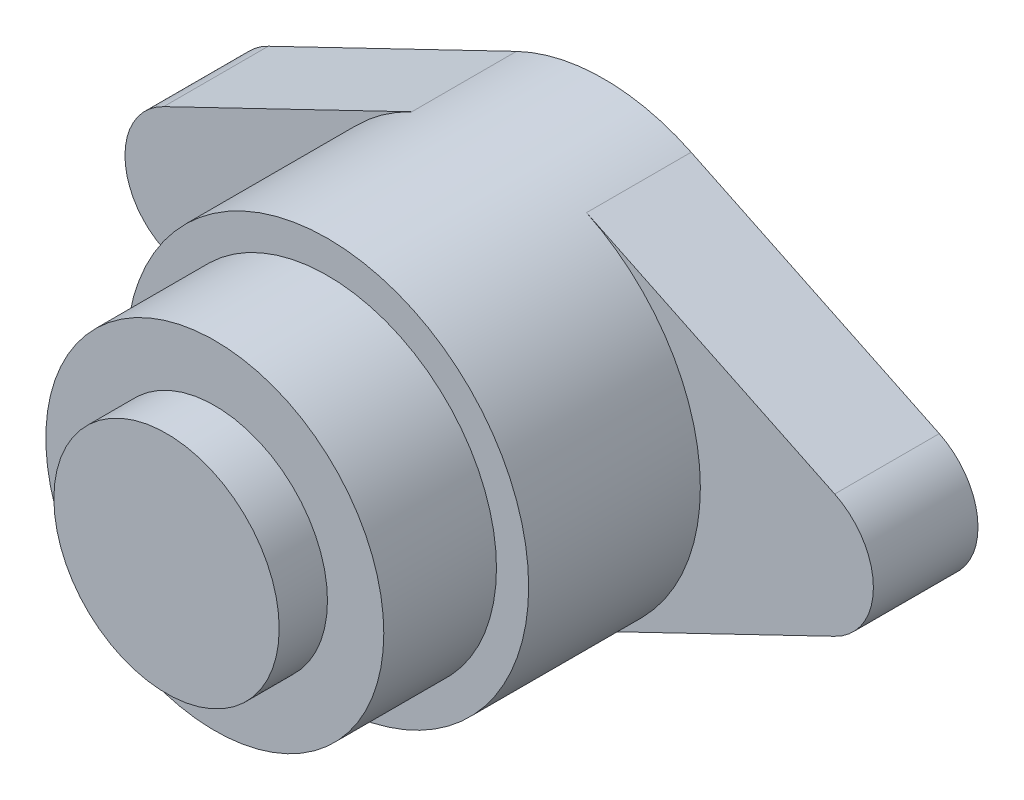
SolidWorks part; units mm, degrees
ref_plane "Front Plane" through (0, 0, 0) normal (0, 0, 1) x (1, 0, 0)
ref_plane "Top Plane" through (0, 0, 0) normal (0, 1, 0) x (1, 0, 0)
ref_plane "Right Plane" through (0, 0, 0) normal (1, 0, 0) x (0, 0, -1)
sketch "Sketch1" plane through (0, 0, 0) normal (0, 0, 1) x (1, 0, 0)
  line L0 (-19, 0) -> (19, 0) construction
  line L1 (-20.8454, 3.8284) -> (-5.4276, 11.2601)
  line L2 (-20.8454, -3.8284) -> (-5.4276, -11.2601)
  line L3 (5.4276, 11.2601) -> (20.8454, 3.8284)
  line L4 (5.4276, -11.2601) -> (20.8454, -3.8284)
  arc A1 (-20.8454, 3.8284) -> (-20.8454, -3.8284) centre (-19, 0) ccw
  arc A2 (20.8454, -3.8284) -> (20.8454, 3.8284) centre (19, 0) ccw
  arc A3 (-5.4276, -11.2601) -> (5.4276, -11.2601) centre (0, 0) ccw
  arc A4 (-5.4276, 11.2601) -> (5.4276, 11.2601) centre (0, 0) cw
  point P0 (0, -12.5)
  point P4 (0, 12.5)
  point P6 (-23.25, 0)
  point P7 (0, 0)
  point P14 (23.25, 0)
  point P17 (0, 0)
  point P18 (0, 0)
  point P19 (0, 0)
  dimension "D1" = 25
  dimension "D2" = 8.5
  dimension "D3" = 46.5
extrude "Boss-Extrude1" add sketch "Sketch1" along normal blind 6.5
sketch "Sketch2" plane through (0, 0, 6.5) normal (0, 0, 1) x (1, 0, 0)
  circle A0 centre (0, 0) radius 12.5
  dimension "D1" = 25
extrude "Boss-Extrude2" add sketch "Sketch2" along normal blind 10.668
sketch "Sketch3" plane through (0, 0, 17.168) normal (0, 0, 1) x (1, 0, 0)
  circle A0 centre (0, 0) radius 10.5
  dimension "D1" = 21
extrude "Boss-Extrude3" add sketch "Sketch3" along normal blind 7
sketch "Sketch4" plane through (0, 0, 24.168) normal (0, 0, 1) x (1, 0, 0)
  circle A0 centre (0, 0) radius 7
  dimension "D1" = 14
extrude "Boss-Extrude4" add sketch "Sketch4" along normal blind 3
